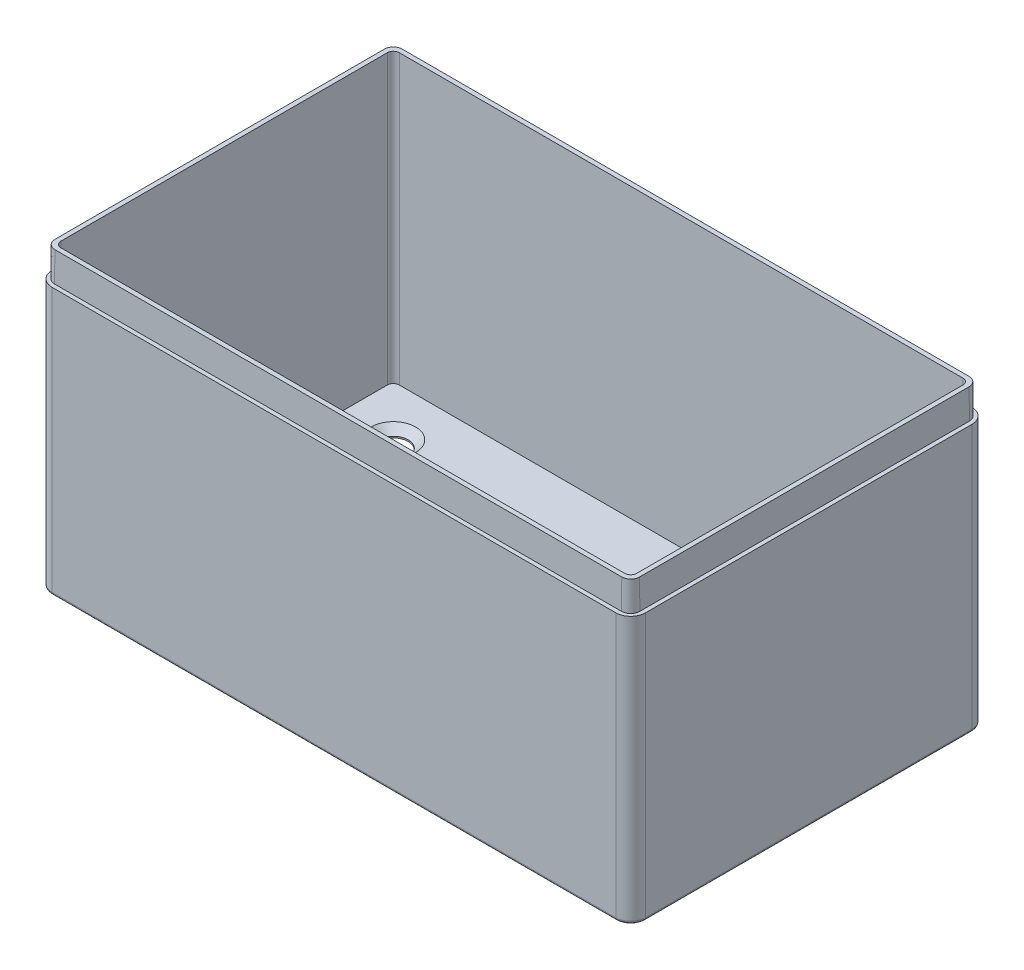
SolidWorks part; units mm, degrees
material "Acrylic (Medium-high impact)"
ref_plane "Front Plane" through (0, 0, 0) normal (0, 0, 1) x (1, 0, 0)
ref_plane "Top Plane" through (0, 0, 0) normal (0, 1, 0) x (1, 0, 0)
ref_plane "Right Plane" through (0, 0, 0) normal (1, 0, 0) x (0, 0, -1)
sketch "Sketch1" plane through (0, 0, 0) normal (0, 1, 0) x (1, 0, 0)
  line L1 (-47.5, -30) -> (47.5, -30)
  line L2 (-50, -27.5) -> (-50, 27.5)
  line L3 (-47.5, 30) -> (47.5, 30)
  line L4 (50, -27.5) -> (50, 27.5)
  line L5 (-50, -30) -> (50, 30) construction
  line L6 (-50, 30) -> (50, -30) construction
  arc A0 (-50, 27.5) -> (-47.5, 30) centre (-47.5, 27.5) cw
  arc A1 (-47.5, -30) -> (-50, -27.5) centre (-47.5, -27.5) cw
  arc A2 (47.5, -30) -> (50, -27.5) centre (47.5, -27.5) ccw
  arc A3 (47.5, 30) -> (50, 27.5) centre (47.5, 27.5) cw
  point P0 (0, 0)
  dimension "D3" = 2.5
  dimension "D1" = 100
  dimension "D2" = 60
extrude "Boss-Extrude1" add sketch "Sketch1" along normal blind 50
shell "Shell1" thickness 1.5
sketch "Sketch2" plane through (0, 1.5, 0) normal (0, 1, 0) x (1, 0, 0)
  line L0 (0, 30) -> (0, -30) construction
  line L1 (47.5, 30) -> (-47.5, 30) construction
  line L2 (-47.5, -30) -> (47.5, -30) construction
  line L3 (-50, 0) -> (50, 0) construction
  line L4 (-50, 27.5) -> (-50, -27.5) construction
  line L5 (50, -27.5) -> (50, 27.5) construction
  circle A0 centre (-40, 20) radius 2.5
  circle A1 centre (40, 20) radius 2.5
  circle A2 centre (40, -20) radius 2.5
  circle A3 centre (-40, -20) radius 2.5
  dimension "D1" = 5
  dimension "D2" = 10
  dimension "D3" = 10
extrude "Cut-Extrude1" cut sketch "Sketch2" against normal blind 50
sketch "Sketch3" plane through (0, 50, 0) normal (0, 1, 0) x (1, 0, 0)
  line L1 (-47.7678, -29.2678) -> (47.7678, -29.2678)
  line L2 (-49.2678, -27.7678) -> (-49.2678, 27.7678)
  line L3 (-47.7678, 29.2678) -> (47.7678, 29.2678)
  line L4 (49.2678, -27.7678) -> (49.2678, 27.7678)
  line L5 (-49.2678, -29.2678) -> (49.2678, 29.2678) construction
  line L6 (-49.2678, 29.2678) -> (49.2678, -29.2678) construction
  arc A0 (50, 27.5) -> (47.5, 30) centre (47.5, 27.5) ccw construction
  arc A1 (-47.7678, -29.2678) -> (-49.2678, -27.7678) centre (-47.7678, -27.7678) cw
  arc A2 (47.7678, -29.2678) -> (49.2678, -27.7678) centre (47.7678, -27.7678) ccw
  arc A3 (47.7678, 29.2678) -> (49.2678, 27.7678) centre (47.7678, 27.7678) cw
  arc A4 (-49.2678, 27.7678) -> (-47.7678, 29.2678) centre (-47.7678, 27.7678) cw
  point P0 (0, 0)
  dimension "D1" = 1.5
extrude "Cut-Extrude2" cut sketch "Sketch3" against normal blind 5 draft 0.5 flip side to cut
fillet "Fillet1" radius 0.5 8 edges at (49.2678, 0, 29.2678) (49.2678, 0, -29.2678) (-49.2678, 0, -29.2678) (-49.2678, 0, 29.2678) (-50, 0, 0) (0, 0, -30) (50, 0, 0) (0, 0, 30)
chamfer "Chamfer1" distance 1.25 angle 45 4 edges at (-40, 1.5, 17.5) (40, 1.5, 22.5) (40, 1.5, -22.5) (-40, 1.5, -17.5)
